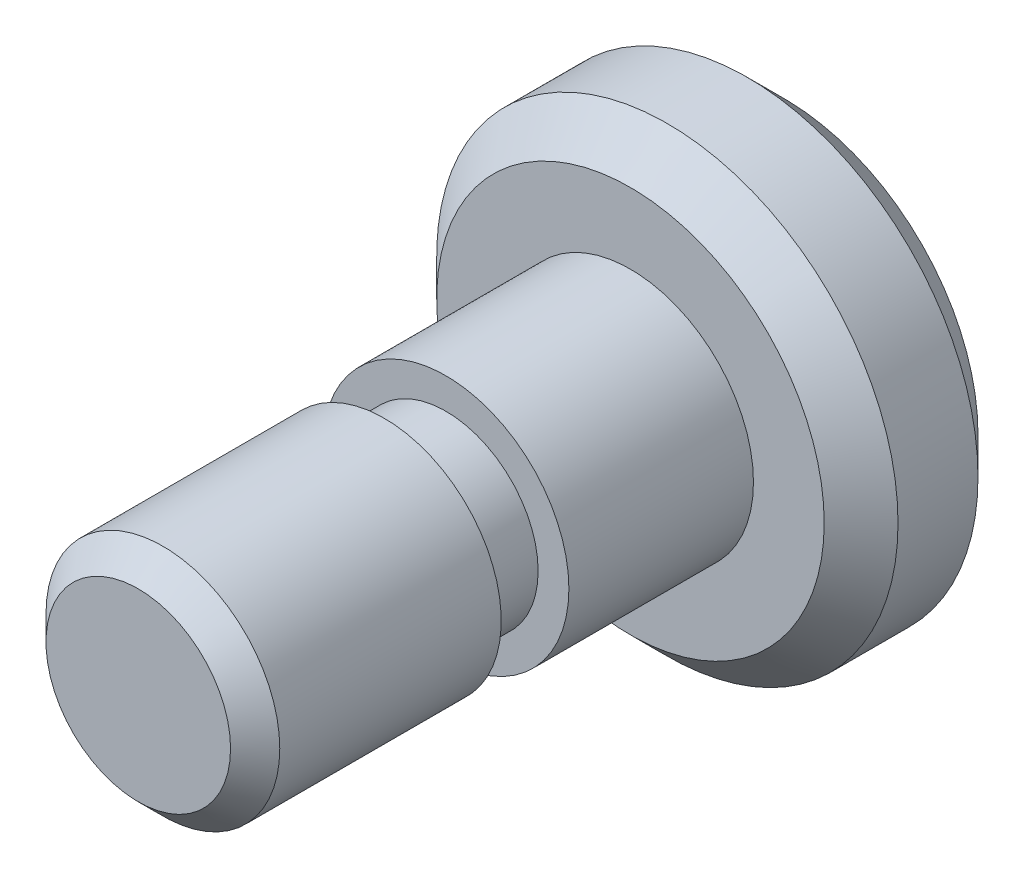
SolidWorks part; units mm, degrees
material "6061-T6 (SS)"
ref_plane "Front" through (0, 0, 0) normal (0, 0, 1) x (1, 0, 0)
ref_plane "Top" through (0, 0, 0) normal (0, 1, 0) x (1, 0, 0)
ref_plane "Right" through (0, 0, 0) normal (1, 0, 0) x (0, 0, -1)
sketch "Centerline" plane through (0, 0, 0) normal (0, 1, 0) x (1, 0, 0)
  line L0 (0, -23.0538) -> (0, -18.702) construction
sketch "Sketch1" plane through (0, 0, 0) normal (0, 0, 1) x (1, 0, 0)
  circle A0 centre (0, 0) radius 4.7625
  dimension "D1" = 9.525
extrude "Boss-Extrude1" add sketch "Sketch1" along normal blind 3.175
sketch "Sketch2" plane through (0, 0, 3.175) normal (0, 0, 1) x (1, 0, 0)
  circle A0 centre (0, 0) radius 2.54
  dimension "D1" = 5.08
extrude "Boss-Extrude2" add sketch "Sketch2" along normal blind 3.81
sketch "Sketch3" plane through (0, 0, 6.985) normal (0, 0, 1) x (1, 0, 0)
  circle A0 centre (0, 0) radius 2.413
  dimension "D1" = 4.826
extrude "Boss-Extrude3" add sketch "Sketch3" along normal blind 6.35
chamfer "Chamfer1" distance 0.508 angle 45 1 edges at (2.413, 0, 13.335)
sketch "Sketch8" plane through (0, 0, 0) normal (0, 1, 0) x (1, 0, 0)
  line L0 (-2.54, -6.985) -> (2.54, -6.985) construction
  line L1 (-2.54, -6.985) -> (-1.905, -6.985)
  line L2 (-2.54, -6.985) -> (-2.54, -8.255)
  line L3 (-2.54, -8.255) -> (-1.905, -8.255)
  line L4 (-1.905, -8.255) -> (-1.905, -6.985)
  line L5 (-1.905, -13.335) -> (1.905, -13.335) construction
  line L6 (-1.905, -13.335) -> (1.905, -13.335) construction
  line L7 (-1.905, -13.335) -> (-1.905, -11.6852) construction
  dimension "D1" = 1.27
revolve "Cut-Revolve1" cut sketch "Sketch8" angle 360 about L0
thread "Thread1" pitch 0.7937 start angle 0, offset 1.27, length 0, pitch 0.7937, diameter 4.826
ref_plane "Plane1" through (-2.413, 0, 14.097) normal (0, -1, 0) x (-1, 0, 0)
sketch "Thread Profile1" plane through (-2.413, 0, 14.097) normal (0, -1, 0) x (-1, 0, 0)
  line L0 (0, 0) -> (0, 0.7937) construction
  line L11 (0, 0) -> (0, 0.6945)
  line L12 (0, 0.6945) -> (-0.4296, 0.4465)
  line L13 (-0.4296, 0.4465) -> (-0.4296, 0.248)
  line L15 (-0.4296, 0.248) -> (0, 0)
  line L17 (-0.4296, 0.3473) -> (0, 0.3473) construction
  point P2 (0, 0)
  dimension "Pitch" = 0.7937
  dimension "Profile_Angle" = 60
  dimension "Profile_Land" = 0.1984
  dimension "Profile_Height" = 0.4296
chamfer "Chamfer2" distance 0.762 angle 45 2 edges at (4.7625, 0, 3.175) (4.7625, 0, 0)
